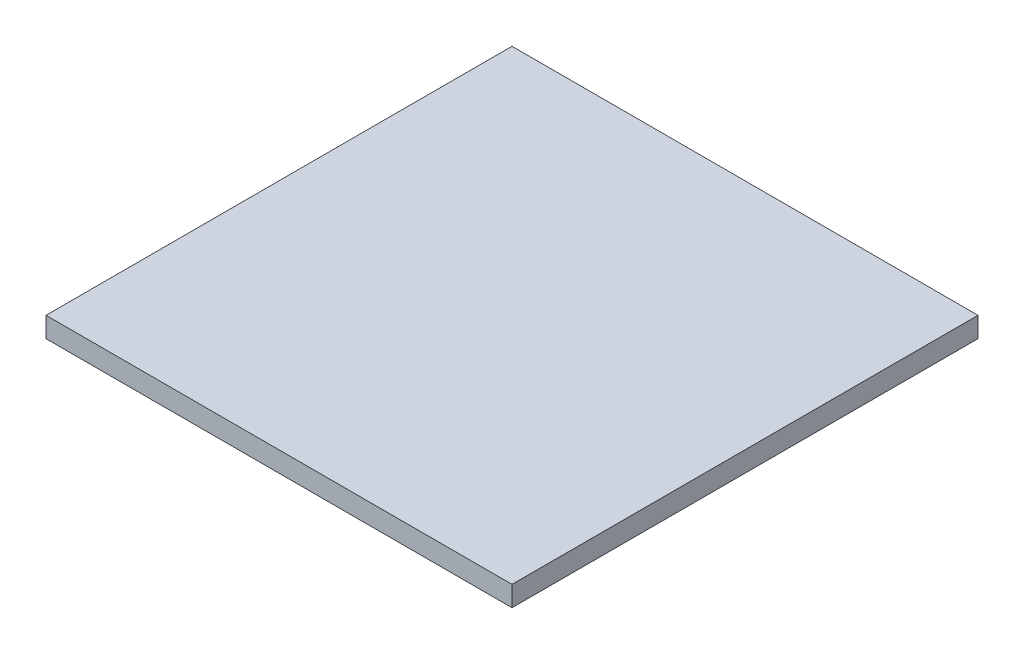
SolidWorks part; units mm, degrees
ref_plane "Front Plane" through (0, 0, 0) normal (0, 0, 1) x (1, 0, 0)
ref_plane "Top Plane" through (0, 0, 0) normal (0, 1, 0) x (1, 0, 0)
ref_plane "Right Plane" through (0, 0, 0) normal (1, 0, 0) x (0, 0, -1)
sketch "Sketch1" plane through (0, 0, 0) normal (0, 1, 0) x (1, 0, 0)
  line L1 (-146.05, 146.05) -> (146.05, 146.05)
  line L2 (-146.05, 146.05) -> (-146.05, -146.05)
  line L3 (-146.05, -146.05) -> (146.05, -146.05)
  line L4 (146.05, 146.05) -> (146.05, -146.05)
  line L5 (-146.05, 146.05) -> (146.05, -146.05) construction
  line L6 (-146.05, -146.05) -> (146.05, 146.05) construction
  point P0 (0, 0)
  dimension "D1" = 292.1
  dimension "D2" = 292.1
extrude "Boss-Extrude1" add sketch "Sketch1" along normal blind 12.7
